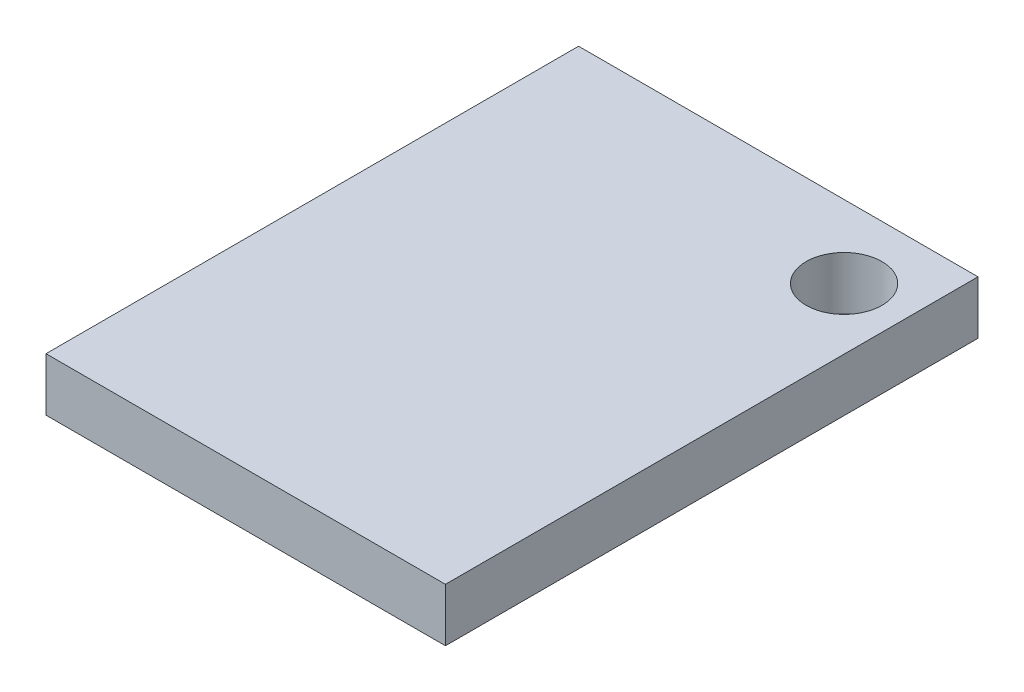
SolidWorks part; units mm, degrees
ref_plane "Front Plane" through (0, 0, 0) normal (0, 0, 1) x (1, 0, 0)
ref_plane "Top Plane" through (0, 0, 0) normal (0, 1, 0) x (1, 0, 0)
ref_plane "Right Plane" through (0, 0, 0) normal (1, 0, 0) x (0, 0, -1)
sketch "Sketch1" plane through (0, 0, 0) normal (0, 1, 0) x (1, 0, 0)
  line L1 (-7.5, 10) -> (7.5, 10)
  line L2 (-7.5, 10) -> (-7.5, -10)
  line L3 (-7.5, -10) -> (7.5, -10)
  line L4 (7.5, 10) -> (7.5, -10)
  line L5 (-7.5, 10) -> (7.5, -10) construction
  line L6 (-7.5, -10) -> (7.5, 10) construction
  point P0 (0, 0)
  dimension "D1" = 20
  dimension "D2" = 15
extrude "Boss-Extrude1" add sketch "Sketch1" along normal blind 2
sketch "Sketch2" plane through (0, 2, 0) normal (0, 1, 0) x (1, 0, 0)
  circle A0 centre (5.201, 7.2696) radius 1.4252
extrude "Cut-Extrude1" cut sketch "Sketch2" against normal through all contours A0
